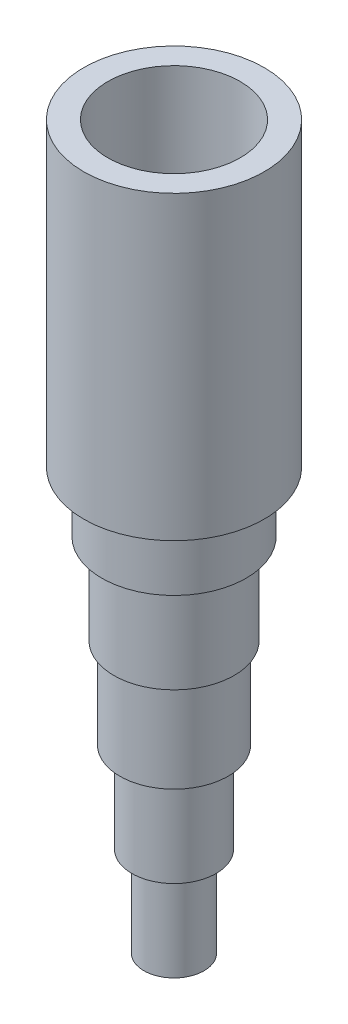
SolidWorks part; units mm, degrees
ref_plane "Front Plane" through (0, 0, 0) normal (0, 0, 1) x (1, 0, 0)
ref_plane "Top Plane" through (0, 0, 0) normal (0, 1, 0) x (1, 0, 0)
ref_plane "Right Plane" through (0, 0, 0) normal (1, 0, 0) x (0, 0, -1)
sketch "Sketch1" plane through (0, 0, 0) normal (0, 0, 1) x (1, 0, 0)
  line L1 (58.9959, 47.3218) -> (58.9959, 15.5718)
  line L6 (52.6459, -28.8782) -> (46.2959, -28.8782)
  line L12 (46.2959, -28.8782) -> (46.2959, -19.3532)
  line L18 (46.2959, -19.3532) -> (52.6459, -19.3532)
  line L24 (46.2959, -19.3532) -> (45.0259, -19.3532)
  line L30 (45.0259, -19.3532) -> (45.0259, -9.8282)
  line L36 (45.0259, -9.8282) -> (53.9159, -9.8282)
  line L38 (45.0259, -9.8282) -> (43.7559, -9.8282)
  line L39 (43.7559, -9.8282) -> (43.7559, -0.3032)
  line L40 (43.7559, -0.3032) -> (55.1859, -0.3032)
  line L41 (43.7559, -0.3032) -> (43.1209, -0.3032)
  line L42 (43.1209, -0.3032) -> (43.1209, 9.2218)
  line L43 (43.1209, 9.2218) -> (55.8209, 9.2218)
  line L44 (43.1209, 9.2218) -> (41.8509, 9.2218)
  line L45 (41.8509, 9.2218) -> (41.8509, 15.5718)
  line L46 (41.8509, 15.5718) -> (57.0909, 15.5718)
  line L47 (41.8509, 15.5718) -> (39.9459, 15.5718)
  line L48 (58.9959, 47.3218) -> (39.9459, 47.3218)
  line L49 (39.9459, 47.3218) -> (39.9459, 15.5718)
  line L50 (49.4709, -38.228) -> (49.4709, 54.8126) construction
  line L51 (57.0909, 15.5718) -> (58.9959, 15.5718)
  line L52 (57.0909, 9.2218) -> (57.0909, 15.5718)
  line L53 (55.8209, 9.2218) -> (57.0909, 9.2218)
  line L54 (55.8209, -0.3032) -> (55.8209, 9.2218)
  line L55 (55.1859, -0.3032) -> (55.8209, -0.3032)
  line L56 (55.1859, -9.8282) -> (55.1859, -0.3032)
  line L57 (53.9159, -9.8282) -> (55.1859, -9.8282)
  line L58 (53.9159, -19.3532) -> (53.9159, -9.8282)
  line L59 (52.6459, -19.3532) -> (53.9159, -19.3532)
  line L60 (52.6459, -28.8782) -> (52.6459, -19.3532)
  point P49 (49.4709, 47.3218)
  point P50 (49.4709, 15.5718)
  point P52 (49.4709, 9.2218)
  point P54 (49.4709, -0.3032)
  point P56 (49.4709, -9.8282)
  point P58 (49.4709, -19.3532)
  point P59 (49.4709, -28.8782)
  dimension "D13" = 9.525
  dimension "D14" = 9.525
  dimension "D15" = 9.525
  dimension "D16" = 9.525
  dimension "D17" = 6.35
  dimension "D18" = 6.35
  dimension "D19" = 76.2
  dimension "D20" = 8.89
  dimension "D21" = 11.43
  dimension "D22" = 12.7
  dimension "D23" = 15.24
  dimension "D24" = 19.05
revolve "Revolve5" add sketch "Sketch1" angle 360 about L50
shell "Shell1" thickness 2.54
